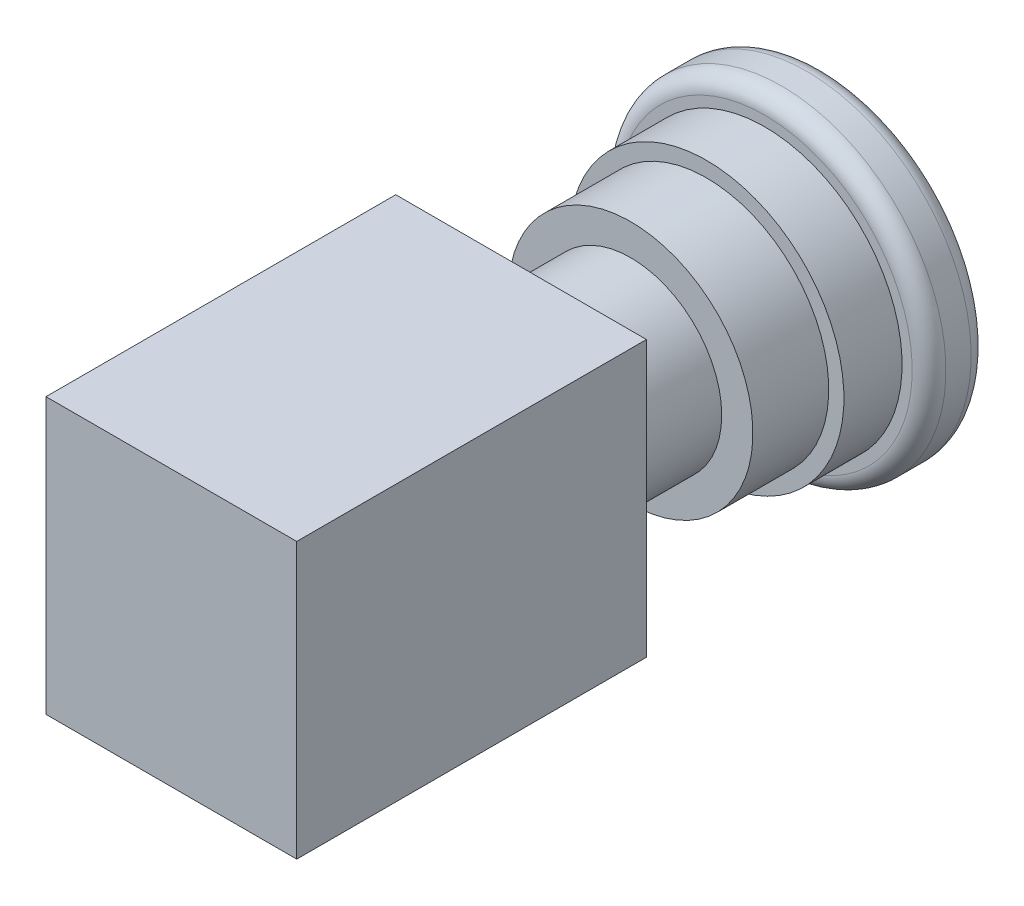
SolidWorks part; units mm, degrees
ref_plane "Front Plane" through (0, 0, 0) normal (0, 0, 1) x (1, 0, 0)
ref_plane "Top Plane" through (0, 0, 0) normal (0, 1, 0) x (1, 0, 0)
ref_plane "Right Plane" through (0, 0, 0) normal (1, 0, 0) x (0, 0, -1)
sketch "Sketch1" plane through (0, 0, 0) normal (0, 0, 1) x (1, 0, 0)
  circle A0 centre (0, 0) radius 10.8
  dimension "D1" = 21.6
extrude "Boss-Extrude1" add sketch "Sketch1" along normal blind 13
sketch "Sketch2" plane through (0, 0, 0) normal (0, 0, -1) x (-1, 0, 0)
  circle A0 centre (0, 0) radius 14.5
  dimension "D1" = 29
extrude "Boss-Extrude2" add sketch "Sketch2" along normal blind 9
sketch "Sketch3" plane through (0, 0, -9) normal (0, 0, -1) x (-1, 0, 0)
  circle A0 centre (0, 0) radius 16.3
  dimension "D1" = 32.6
extrude "Boss-Extrude3" add sketch "Sketch3" along normal blind 6.9
sketch "Sketch4" plane through (0, 0, -15.9) normal (0, 0, -1) x (-1, 0, 0)
  circle A0 centre (0, 0) radius 19.5
  dimension "D1" = 39
extrude "Boss-Extrude4" add sketch "Sketch4" along normal blind 7
fillet "Fillet1" radius 2 2 edges at (-19.5, 0, -15.9) (-19.5, 0, -22.9)
sketch "Sketch5" plane through (0, 0, 13) normal (0, 0, 1) x (1, 0, 0)
  line L1 (-14.875, -16.325) -> (14.875, -16.325)
  line L2 (-14.875, -16.325) -> (-14.875, 16.325)
  line L3 (-14.875, 16.325) -> (14.875, 16.325)
  line L4 (14.875, -16.325) -> (14.875, 16.325)
  line L5 (-14.875, -16.325) -> (14.875, 16.325) construction
  line L6 (-14.875, 16.325) -> (14.875, -16.325) construction
  point P0 (0, 0)
  dimension "D1" = 29.75
  dimension "D2" = 32.65
extrude "Boss-Extrude5" add sketch "Sketch5" along normal blind 41.5
